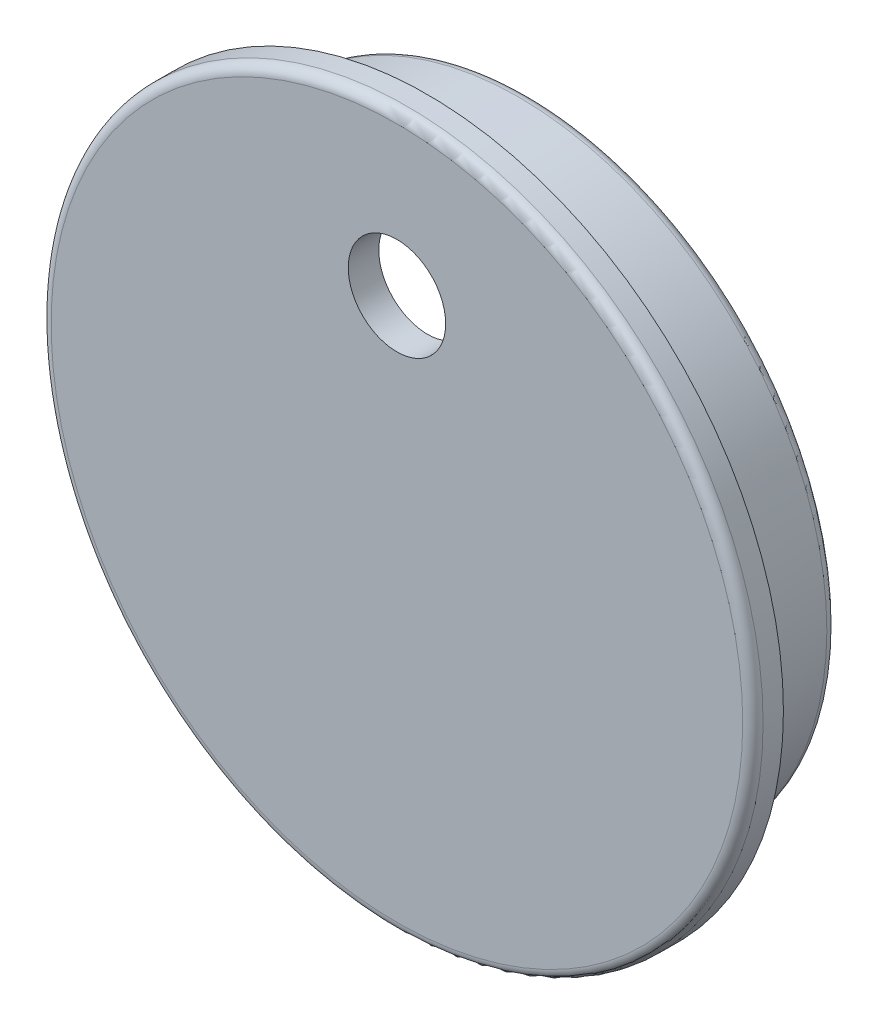
SolidWorks part; units mm, degrees
ref_plane "Front Plane" through (0, 0, 0) normal (0, 0, 1) x (1, 0, 0)
ref_plane "Top Plane" through (0, 0, 0) normal (0, 1, 0) x (1, 0, 0)
ref_plane "Right Plane" through (0, 0, 0) normal (1, 0, 0) x (0, 0, -1)
sketch "Sketch1" plane through (0, 0, 0) normal (0, 0, 1) x (1, 0, 0)
  circle A1 centre (0, 0) radius 44.45
  circle A2 centre (0, 0) radius 44.45
  dimension "D1" = 0
extrude "Boss-Extrude1" add sketch "Sketch1" along normal blind 3.81
sketch "Sketch2" plane through (0, 0, 0) normal (0, 0, -1) x (-1, 0, 0)
  circle A1 centre (0, 0) radius 34.6329
  circle A2 centre (0, 0) radius 38.4429
  circle A3 centre (0, 0) radius 38.4429
  dimension "D1" = 0.1905
  dimension "D2" = 3.81
extrude "Boss-Extrude2" add sketch "Sketch2" along normal blind 12.7
fillet "Fillet1" radius 1.27 4 edges at (-34.6329, 0, 0) (-34.6329, 0, -12.7) (-38.4429, 0, -12.7) (44.45, 0, 3.81)
sketch "Sketch4" plane through (0, 0, 3.81) normal (0, 0, 1) x (1, 0, 0)
  circle A3 centre (0, 24.5999) radius 6.0833
  circle A4 centre (0, 24.5999) radius 6.0833
  dimension "D1" = 0.381
extrude "Cut-Extrude1" cut sketch "Sketch4" against normal through all
